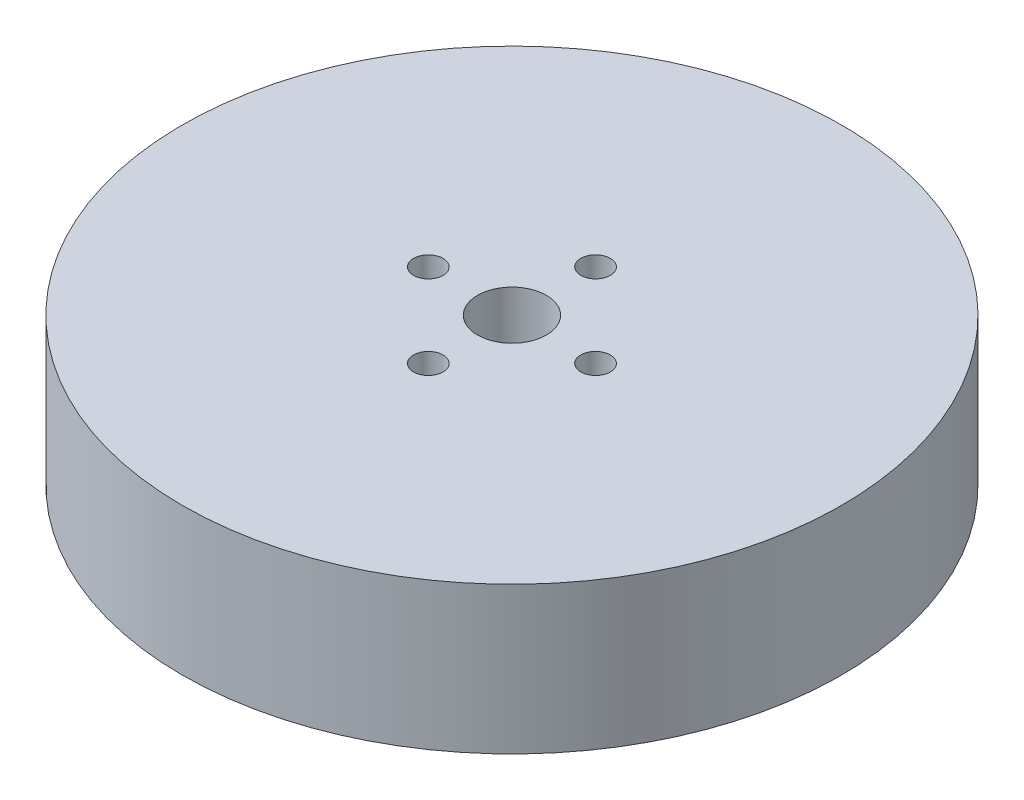
SolidWorks part; units mm, degrees
material "3.0205 (EN-AW 1200)"
ref_plane "Front Plane" through (0, 0, 0) normal (0, 0, 1) x (1, 0, 0)
ref_plane "Top Plane" through (0, 0, 0) normal (0, 1, 0) x (1, 0, 0)
ref_plane "Right Plane" through (0, 0, 0) normal (1, 0, 0) x (0, 0, -1)
sketch "Sketch1" plane through (0, 0, 0) normal (0, 1, 0) x (1, 0, 0)
  circle A0 centre (0, 0) radius 33.5
extrude "Boss-Extrude1" add sketch "Sketch1" along normal blind 17
sketch "Sketch2" plane through (0, 0, 0) normal (0, 1, 0) x (1, 0, 0)
  circle A0 centre (0, 0) radius 3.5
extrude "Cut-Extrude1" cut sketch "Sketch2" against normal blind 100 and the other way blind 100
sketch "Sketch3" plane through (0, 0, 0) normal (0, 1, 0) x (1, 0, 0)
  circle A0 centre (0, 0) radius 33.5 construction
  circle A1 centre (8.5, 0) radius 1.5
  circle A2 centre (-8.5, 0) radius 1.5
  circle A3 centre (0, -8.5) radius 1.5
  circle A4 centre (0, 8.5) radius 1.5
  dimension "D1" = 8.5
extrude "Cut-Extrude2" cut sketch "Sketch3" against normal blind 100 and the other way blind 100
chamfer "Chamfer1" distance 13 angle 9 1 edges at (0, 0, 33.5)
